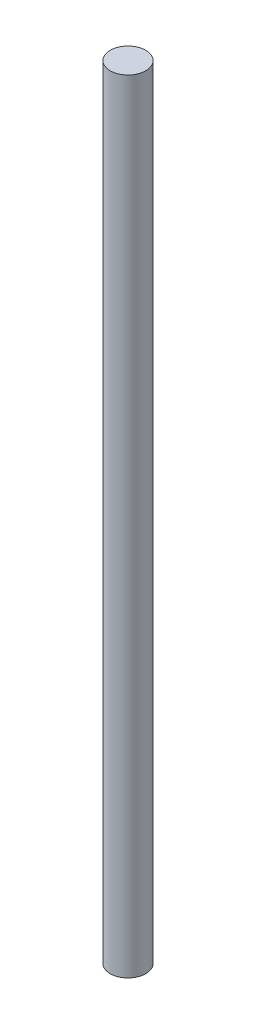
SolidWorks part; units mm, degrees
ref_plane "Front Plane" through (0, 0, 0) normal (0, 0, 1) x (1, 0, 0)
ref_plane "Top Plane" through (0, 0, 0) normal (0, 1, 0) x (1, 0, 0)
ref_plane "Right Plane" through (0, 0, 0) normal (1, 0, 0) x (0, 0, -1)
sketch "Sketch1" plane through (0, 0, 0) normal (0, 1, 0) x (1, 0, 0)
  circle A0 centre (0, 0) radius 3.175
  dimension "D1" = 6.35
extrude "Boss-Extrude1" add sketch "Sketch1" along normal blind 139.7
